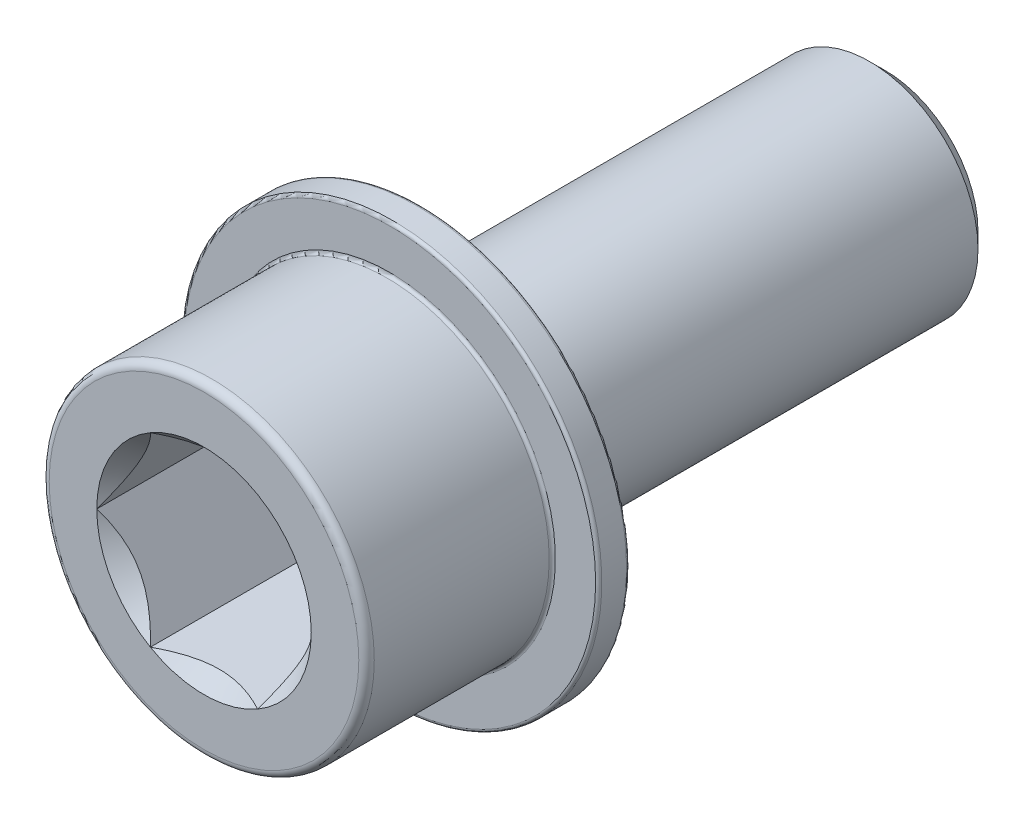
SolidWorks part; units mm, degrees
material "Acciaio inossidabile (ferroso)"
ref_plane "Piano frontale" through (0, 0, 0) normal (0, 0, 1) x (1, 0, 0)
ref_plane "Piano superiore" through (0, 0, 0) normal (0, 1, 0) x (1, 0, 0)
ref_plane "Piano destro" through (0, 0, 0) normal (1, 0, 0) x (0, 0, -1)
sketch "Schizzo1" plane through (0, 0, 0) normal (0, 0, 1) x (1, 0, 0)
  circle A0 centre (0, 0) radius 7
  dimension "D1" = 14
extrude "Estrusione-Estrusione1" add sketch "Schizzo1" along normal blind 30
cosmetic thread "Filettatura cosmetica2" parameters "D2"=11.797
chamfer "Smusso1" distance 1 angle 45 1 edges at (7, 0, 0)
sketch "Schizzo6" plane through (0, 0, 30) normal (0, 0, 1) x (1, 0, 0)
  circle A0 centre (0, 0) radius 10.5
  dimension "D1" = 21
extrude "Estrusione-Estrusione3" add sketch "Schizzo6" along normal blind 14
sketch "Schizzo7" plane through (0, 0, 44) normal (0, 0, 1) x (1, 0, 0)
  line L1 (3.4641, 6) -> (-3.4641, 6)
  line L2 (-3.4641, 6) -> (-6.9282, 0)
  line L3 (-6.9282, 0) -> (-3.4641, -6)
  line L4 (-3.4641, -6) -> (3.4641, -6)
  line L5 (3.4641, -6) -> (6.9282, 0)
  line L6 (6.9282, 0) -> (3.4641, 6)
  circle A1 centre (0, 0) radius 6 construction
  dimension "D1" = 12
extrude "Taglio-Estrusione3" cut sketch "Schizzo7" against normal blind 10
sketch "Schizzo8" plane through (0, 0, 44) normal (0, 0, 1) x (1, 0, 0)
  circle A0 centre (0, 0) radius 6.9282
extrude "Taglio-Estrusione4" cut sketch "Schizzo8" against normal blind 1 draft 43
fillet "Raccordo5" radius 0.5 1 edges at (10.5, 0, 44)
sketch "Schizzo9" plane through (0, 0, 30) normal (0, 0, -1) x (-1, 0, 0)
  circle A0 centre (0, 0) radius 10.5 construction
  circle A1 centre (0, 0) radius 10.5
  circle A2 centre (0, 0) radius 13.5
  dimension "D1" = 27
extrude "Estrusione-Estrusione4" add sketch "Schizzo9" against normal blind 2
fillet "Raccordo6" radius 0.2 3 edges at (-10.5, 0, 32) (-13.5, 0, 32) (-13.5, 0, 30)
